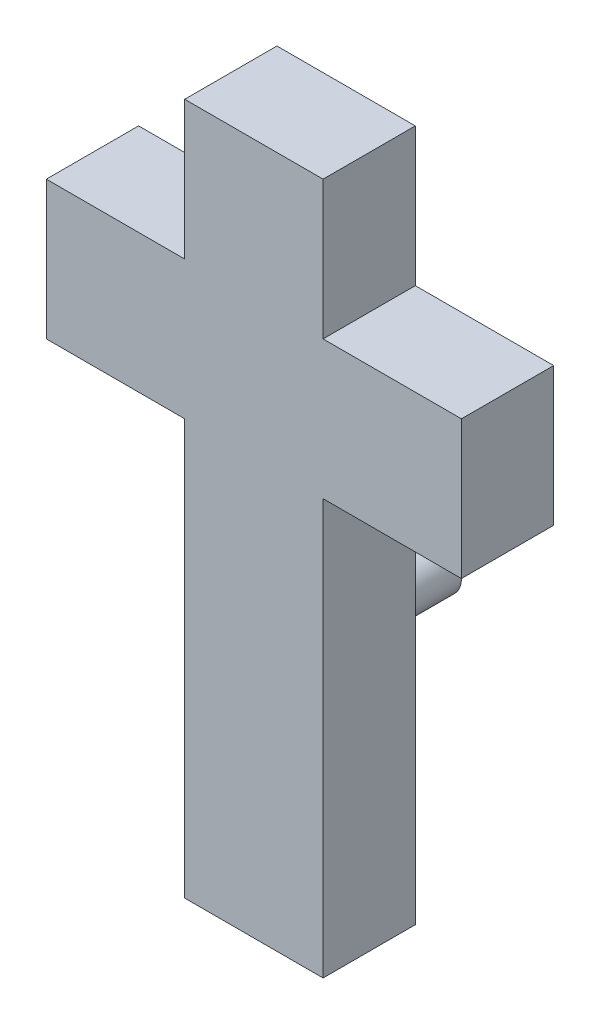
SolidWorks part; units mm, degrees
ref_plane "Front Plane" through (0, 0, 0) normal (0, 0, 1) x (1, 0, 0)
ref_plane "Top Plane" through (0, 0, 0) normal (0, 1, 0) x (1, 0, 0)
ref_plane "Right Plane" through (0, 0, 0) normal (1, 0, 0) x (0, 0, -1)
sketch "Sketch1" plane through (0, 0, 0) normal (0, 0, 1) x (1, 0, 0)
  line L0 (0, 0) -> (0, 22.86)
  line L1 (0, 22.86) -> (-7.62, 22.86)
  line L2 (-7.62, 22.86) -> (-7.62, 30.48)
  line L3 (-7.62, 30.48) -> (0, 30.48)
  line L4 (0, 30.48) -> (0, 38.1)
  line L5 (0, 38.1) -> (7.62, 38.1)
  line L6 (7.62, 38.1) -> (7.62, 30.48)
  line L7 (7.62, 30.48) -> (15.24, 30.48)
  line L8 (15.24, 30.48) -> (15.24, 22.86)
  line L9 (15.24, 22.86) -> (7.62, 22.86)
  line L10 (7.62, 22.86) -> (7.62, 0)
  line L11 (7.62, 0) -> (0, 0)
  dimension "D1" = 7.62
  dimension "D2" = 7.62
  dimension "D3" = 7.62
  dimension "D4" = 7.62
  dimension "D5" = 7.62
  dimension "D6" = 7.62
  dimension "D7" = 22.86
  dimension "D8" = 7.62
  dimension "D9" = 22.86
extrude "Boss-Extrude1" add sketch "Sketch1" along normal blind 5.08 contours L3 L4 L5 L6 L7 L8 L9 L10 L11 L0 L1 L2
sketch "Sketch2" plane through (0, 0, 0) normal (0, 0, -1) x (-1, 0, 0)
  line L0 (-3.81, 38.1) -> (-3.81, 0) construction
  line L1 (0, 38.1) -> (-7.62, 38.1) construction
  line L2 (-7.62, 0) -> (0, 0) construction
  circle A0 centre (-3.81, 20.32) radius 1.27
  circle A1 centre (-3.81, 12.7) radius 1.27
  dimension "D1" = 2.54
  dimension "D2" = 2.54
  dimension "D3" = 7.62
  dimension "D4" = 12.7
extrude "Boss-Extrude2" add sketch "Sketch2" along normal blind 5.08
equation "\"cross_size\"=0.3"
equation "\"D1@Sketch1\"=\"cross_size\""
equation "\"D2@Sketch1\"= \"cross_size\""
equation "\"D3@Sketch1\"=\"cross_size\""
equation "\"D5@Sketch1\"=\"cross_size\""
equation "\"D6@Sketch1\"=\"cross_size\""
equation "\"D8@Sketch1\"=\"cross_size\""
equation "\"D9@Sketch1\"=\"cross_size\"*3"
equation "\"D7@Sketch1\"=\"cross_size\"*3"
equation "\"D4@Sketch1\"= \"cross_size\""
